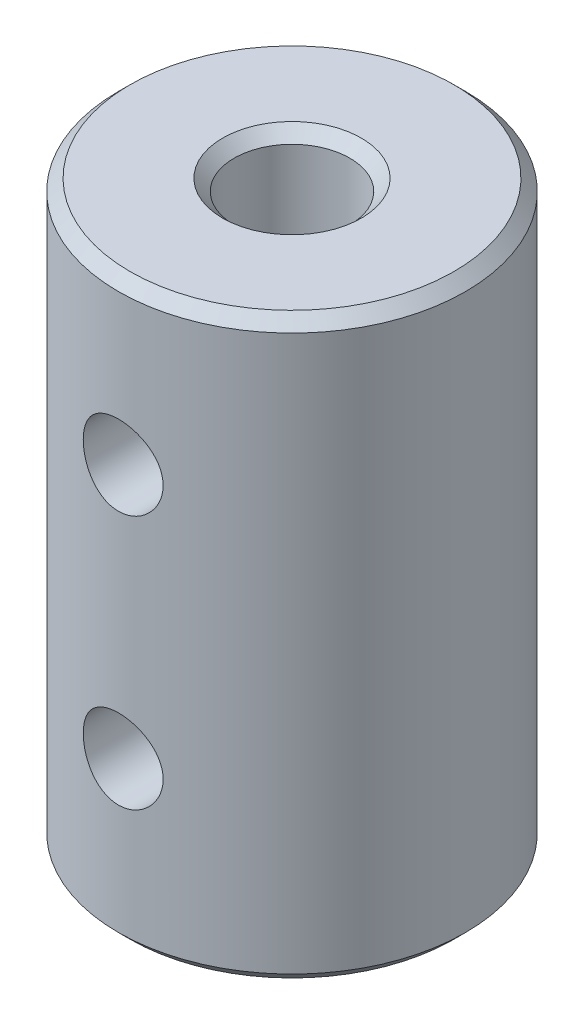
SolidWorks part; units mm, degrees
material "6061-T4 (SS)"
ref_plane "Front Plane" through (0, 0, 0) normal (0, 0, 1) x (1, 0, 0)
ref_plane "Top Plane" through (0, 0, 0) normal (0, 1, 0) x (1, 0, 0)
ref_plane "Right Plane" through (0, 0, 0) normal (1, 0, 0) x (0, 0, -1)
sketch "Sketch1" plane through (0, 0, 0) normal (0, 1, 0) x (1, 0, 0)
  circle A0 centre (0, 0) radius 2.5
  circle A1 centre (0, 0) radius 7.5
  dimension "D1" = 5
  dimension "D2" = 15
extrude "Boss-Extrude1" add sketch "Sketch1" along normal blind 25
chamfer "Chamfer1" distance 0.5 angle 45 4 edges at (0, 0, 2.5) (0, 0, 7.5) (0, 25, 2.5) (0, 25, 7.5)
ref_plane "Plane1" through (0, 0, 19.05) normal (0, 0, 1) x (1, 0, 0)
hole_wizard "#8-32 Tapped Hole1" positions "Sketch3" profile "Sketch4" tap size "#8-32" standard "ANSI Inch"
sketch "Sketch3" plane through (0, 0, 19.05) normal (0, 0, 1) x (1, 0, 0)
  line L0 (-7, 0) -> (7, 0) construction
  point P0 (0, 18)
  point P2 (0, 7)
  dimension "D1" = 7
  dimension "D2" = 11
cosmetic thread "Hole Thread1" parameters "D1"=16.32, "D2"=4.1656
cosmetic thread "Hole Thread2" parameters "D1"=16.32, "D2"=4.1656
sketch "Sketch4" plane through (0, 18, 19.05) normal (1, 0, 0) x (0, -1, 0)
  line L0 (0, 0) -> (0, 19.0378)
  line L1 (0, 19.0378) -> (1.7272, 18)
  line L2 (1.7272, 18) -> (1.7272, 0)
  line L5 (1.7272, 0) -> (0, 0)
  line L10 (0, 19.0378) -> (-1.7272, 18) construction
  line L11 (0, -6.35) -> (0, 107.95) construction
  dimension "Tap Drill Dia." = 3.4544
  dimension "Tap Drill Depth" = 18
  dimension "Drill Angle" = 118
